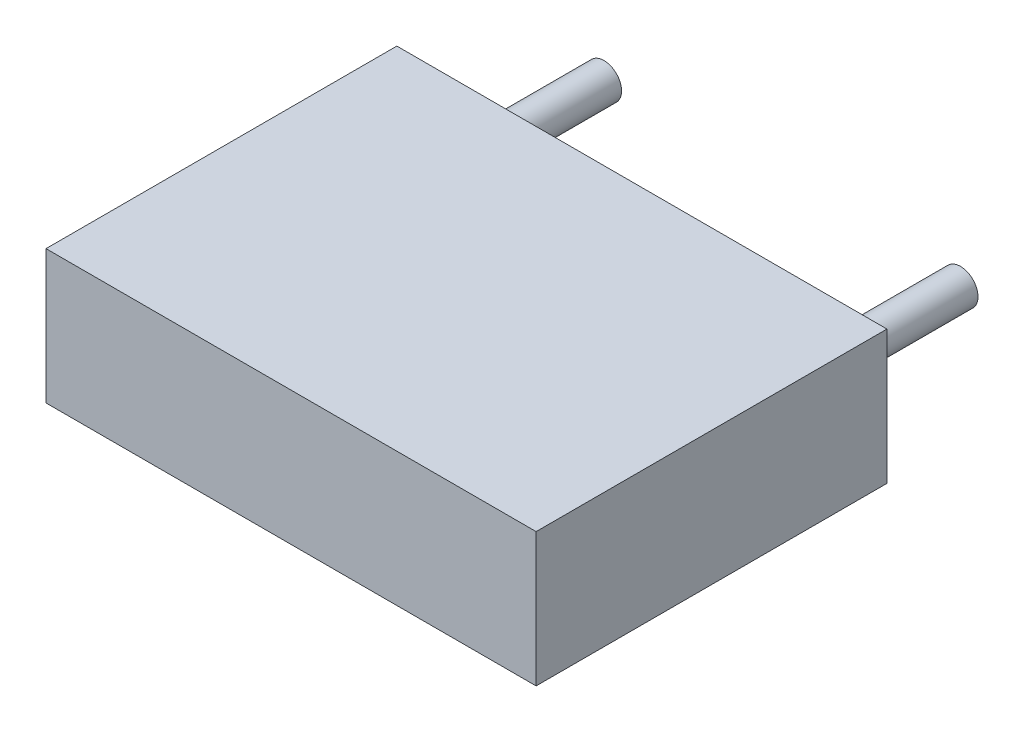
SolidWorks part; units mm, degrees
ref_plane "Front Plane" through (0, 0, 0) normal (0, 0, 1) x (1, 0, 0)
ref_plane "Top Plane" through (0, 0, 0) normal (0, 1, 0) x (1, 0, 0)
ref_plane "Right Plane" through (0, 0, 0) normal (1, 0, 0) x (0, 0, -1)
sketch "Sketch1" plane through (0, 0, 0) normal (0, 0, 1) x (1, 0, 0)
  line L0 (-0.9525, 0.9525) -> (-0.9525, -0.9525)
  line L1 (-0.9525, -0.9525) -> (6.0325, -0.9525)
  line L2 (6.0325, -0.9525) -> (6.0325, 0.9525)
  line L3 (6.0325, 0.9525) -> (-0.9525, 0.9525)
extrude "Component_Outline" add sketch "Sketch1" along normal blind 5 separate body
sketch "Sketch2" plane through (0, 0, 0) normal (0, 0, 1) x (1, 0, 0)
  circle A0 centre (0, 0) radius 0.25
extrude "1" add sketch "Sketch2" against normal blind 2 separate body
sketch "Sketch3" plane through (0, 0, 0) normal (0, 0, 1) x (1, 0, 0)
  circle A0 centre (5.08, 0) radius 0.25
extrude "2" add sketch "Sketch3" against normal blind 2 separate body
sketch3d "3DSketch1"
  line L0 (0, 0, 0) -> (1, 0, 0)
  line L1 (0, 0, 0) -> (0, 1, 0)
  line L2 (0, 0, 0) -> (0, 0, 1)
  point P0 (0, 0, 0)
